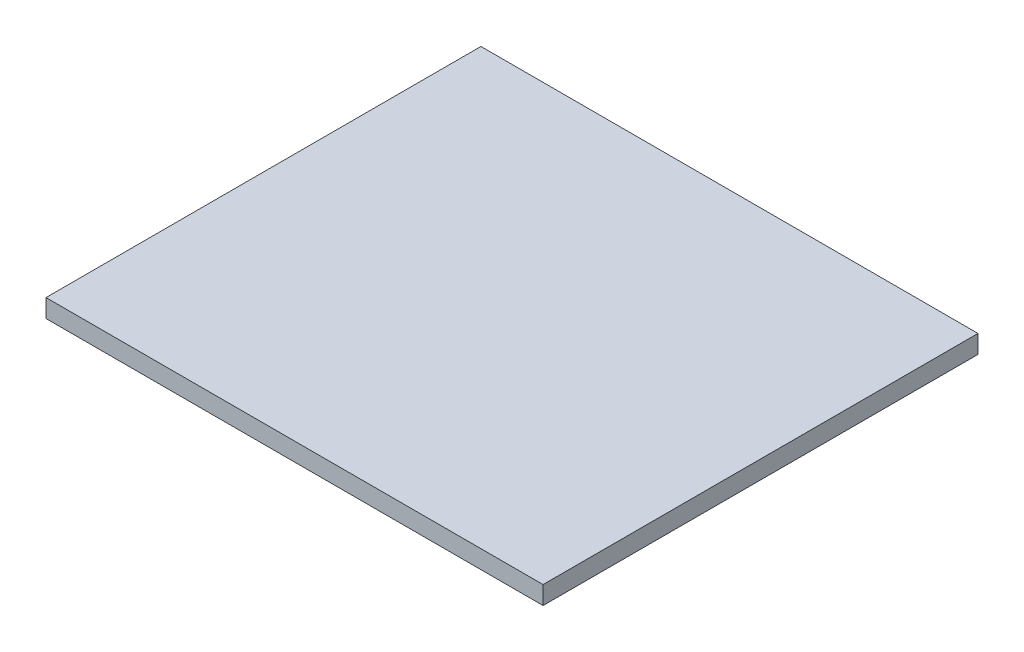
SolidWorks part; units mm, degrees
material "Silicon"
ref_plane "Front Plane" through (0, 0, 0) normal (0, 0, 1) x (1, 0, 0)
ref_plane "Top Plane" through (0, 0, 0) normal (0, 1, 0) x (1, 0, 0)
ref_plane "Right Plane" through (0, 0, 0) normal (1, 0, 0) x (0, 0, -1)
sketch "Sketch1" plane through (0, 0, 0) normal (0, 1, 0) x (1, 0, 0)
  line L1 (-4.1, 3.5875) -> (4.1, 3.5875)
  line L2 (-4.1, 3.5875) -> (-4.1, -3.5875)
  line L3 (-4.1, -3.5875) -> (4.1, -3.5875)
  line L4 (4.1, 3.5875) -> (4.1, -3.5875)
  line L5 (-4.1, 3.5875) -> (4.1, -3.5875) construction
  line L6 (-4.1, -3.5875) -> (4.1, 3.5875) construction
  point P0 (0, 0)
  dimension "D1" = 8.2
  dimension "D2" = 7.175
extrude "Extrude1" add sketch "Sketch1" along normal blind 0.3
